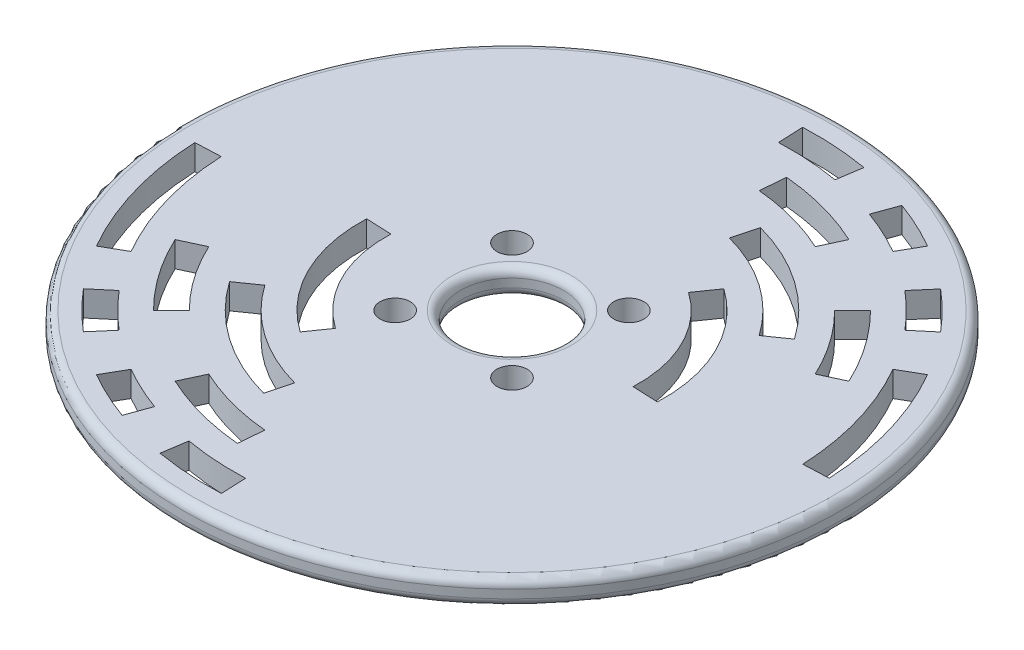
SolidWorks part; units mm, degrees
ref_plane "Front Plane" through (0, 0, 0) normal (0, 0, 1) x (1, 0, 0)
ref_plane "Top Plane" through (0, 0, 0) normal (0, 1, 0) x (1, 0, 0)
ref_plane "Right Plane" through (0, 0, 0) normal (1, 0, 0) x (0, 0, -1)
sketch "Sketch1" plane through (0, 0, 0) normal (0, 1, 0) x (1, 0, 0)
  line L0 (0, 0) -> (8.1776, 8.1776) construction
  circle A0 centre (0, 0) radius 6.096
  circle A1 centre (6.9148, 6.9148) radius 1.7859
  circle A2 centre (6.9148, -6.9148) radius 1.7859
  circle A3 centre (-6.9148, -6.9148) radius 1.7859
  circle A4 centre (-6.9148, 6.9148) radius 1.7859
  point P18 (0, 0)
  dimension "D2" = 3.5719
  dimension "D3" = 4
sketch "Sketch3" plane through (0, 0, 0) normal (0, 1, 0) x (1, 0, 0)
  line L0 (0, -36) -> (0, 36) construction
  line L2 (-36, 0) -> (36, 0) construction
  line L8 (8.6036, 12.2873) -> (10.3244, 14.7447) construction
  line L15 (32.9686, 1.4394) -> (35.9657, 1.5703)
  line L17 (-1.5703, 35.9657) -> (-1.4394, 32.9686)
  line L18 (6.1868, 35.4644) -> (5.7304, 32.4987)
  line L19 (12.3127, 33.8289) -> (11.2867, 31.0099)
  line L20 (18, 31.1769) -> (16.5, 28.5788)
  line L23 (14.9857, -0.6543) -> (17.9829, -0.7851) construction
  line L24 (23.1635, 27.5582) -> (21.212, 25.2795)
  line L25 (27.5776, 23.1404) -> (25.2795, 21.212)
  line L26 (31.1769, 18) -> (28.5788, 16.5)
  line L28 (14.9857, -0.6543) -> (17.9829, -0.7851)
  line L29 (11.2867, 31.0099) -> (12.3127, 33.8289) construction
  line L30 (10.3244, 14.7447) -> (8.6036, 12.2873)
  line L32 (16.5, 28.5788) -> (18, 31.1769) construction
  line L34 (23.3345, 23.3345) -> (25.4558, 25.4558) construction
  line L35 (25.2795, 21.212) -> (27.5776, 23.1404) construction
  line L36 (28.5788, 16.5) -> (31.1769, 18) construction
  line L37 (32.9686, 1.4394) -> (35.9657, 1.5703) construction
  line L38 (2.6147, 29.8858) -> (2.3532, 26.8973)
  line L39 (12.6785, 27.1892) -> (11.4107, 24.4703)
  line L40 (21.2132, 21.2132) -> (19.0919, 19.0919)
  line L41 (27.1892, 12.6785) -> (24.4703, 11.4107)
  line L42 (24.4703, 11.4107) -> (27.1892, 12.6785) construction
  line L43 (2.3532, 26.8973) -> (2.6147, 29.8858) construction
  line L44 (6.2117, 23.1822) -> (5.4352, 20.2844)
  line L45 (19.6596, 13.7658) -> (17.2022, 12.0451)
  line L46 (19.0919, 19.0919) -> (21.2132, 21.2132) construction
  line L47 (17.2022, 12.0451) -> (19.6596, 13.7658) construction
  line L48 (5.4352, 20.2844) -> (6.2117, 23.1822) construction
  line L49 (11.4107, 24.4703) -> (12.6785, 27.1892) construction
  line L64 (1.4394, -32.9686) -> (1.5703, -35.9657) construction
  line L65 (-8.6036, -12.2873) -> (-10.3244, -14.7447) construction
  line L67 (-11.2867, -31.0099) -> (-12.3127, -33.8289) construction
  line L68 (-16.5, -28.5788) -> (-18, -31.1769) construction
  line L69 (-23.3345, -23.3345) -> (-25.4558, -25.4558) construction
  line L70 (-25.2795, -21.212) -> (-27.5776, -23.1404) construction
  line L71 (-28.5788, -16.5) -> (-31.1769, -18) construction
  line L72 (-32.9686, -1.4394) -> (-35.9657, -1.5703) construction
  line L73 (-24.4703, -11.4107) -> (-27.1892, -12.6785) construction
  line L74 (-2.3532, -26.8973) -> (-2.6147, -29.8858) construction
  line L75 (-19.0919, -19.0919) -> (-21.2132, -21.2132) construction
  line L76 (-17.2022, -12.0451) -> (-19.6596, -13.7658) construction
  line L77 (-5.4352, -20.2844) -> (-6.2117, -23.1822) construction
  line L78 (-11.4107, -24.4703) -> (-12.6785, -27.1892) construction
  line L79 (-1.4394, -32.9686) -> (-1.5703, -35.9657) construction
  line L80 (-32.9686, -1.4394) -> (-35.9657, -1.5703)
  line L81 (1.5703, -35.9657) -> (1.4394, -32.9686)
  line L82 (-6.1868, -35.4644) -> (-5.7304, -32.4987)
  line L83 (-12.3127, -33.8289) -> (-11.2867, -31.0099)
  line L84 (-18, -31.1769) -> (-16.5, -28.5788)
  line L85 (-23.1635, -27.5582) -> (-21.212, -25.2795)
  line L86 (-27.5776, -23.1404) -> (-25.2795, -21.212)
  line L87 (-31.1769, -18) -> (-28.5788, -16.5)
  line L88 (-14.9857, 0.6543) -> (-17.9829, 0.7851)
  line L89 (-10.3244, -14.7447) -> (-8.6036, -12.2873)
  line L90 (-2.6147, -29.8858) -> (-2.3532, -26.8973)
  line L91 (-12.6785, -27.1892) -> (-11.4107, -24.4703)
  line L92 (-21.2132, -21.2132) -> (-19.0919, -19.0919)
  line L93 (-27.1892, -12.6785) -> (-24.4703, -11.4107)
  line L94 (-6.2117, -23.1822) -> (-5.4352, -20.2844)
  line L95 (-19.6596, -13.7658) -> (-17.2022, -12.0451)
  arc A0 (14.9857, -0.6543) -> (8.6036, 12.2873) centre (0, 0) ccw
  arc A1 (17.9829, -0.7851) -> (10.3244, 14.7447) centre (0, 0) ccw
  arc A4 (24.4703, 11.4107) -> (19.0919, 19.0919) centre (0, 0) ccw
  arc A5 (27.1892, 12.6785) -> (21.2132, 21.2132) centre (0, 0) ccw
  arc A6 (32.9686, 1.4394) -> (28.5788, 16.5) centre (0, 0) ccw
  arc A7 (35.9657, 1.5703) -> (31.1769, 18) centre (0, 0) ccw
  arc A8 (25.2795, 21.212) -> (21.212, 25.2795) centre (0, 0) ccw
  arc A9 (27.5776, 23.1404) -> (23.1635, 27.5582) centre (0, 0) ccw
  arc A10 (18, 31.1769) -> (12.3127, 33.8289) centre (0, 0) ccw
  arc A11 (16.5, 28.5788) -> (11.2867, 31.0099) centre (0, 0) ccw
  arc A12 (6.1868, 35.4644) -> (-1.5703, 35.9657) centre (0, 0) ccw
  arc A13 (5.7304, 32.4987) -> (-1.4394, 32.9686) centre (0, 0) ccw
  arc A14 (17.2022, 12.0451) -> (5.4352, 20.2844) centre (0, 0) ccw
  arc A15 (19.6596, 13.7658) -> (6.2117, 23.1822) centre (0, 0) ccw
  arc A16 (11.4107, 24.4703) -> (2.3532, 26.8973) centre (0, 0) ccw
  arc A17 (12.6785, 27.1892) -> (2.6147, 29.8858) centre (0, 0) ccw
  arc A32 (-14.9857, 0.6543) -> (-8.6036, -12.2873) centre (0, 0) ccw
  arc A33 (-17.9829, 0.7851) -> (-10.3244, -14.7447) centre (0, 0) ccw
  arc A34 (-24.4703, -11.4107) -> (-19.0919, -19.0919) centre (0, 0) ccw
  arc A35 (-27.1892, -12.6785) -> (-21.2132, -21.2132) centre (0, 0) ccw
  arc A36 (-32.9686, -1.4394) -> (-28.5788, -16.5) centre (0, 0) ccw
  arc A37 (-35.9657, -1.5703) -> (-31.1769, -18) centre (0, 0) ccw
  arc A38 (-25.2795, -21.212) -> (-21.212, -25.2795) centre (0, 0) ccw
  arc A39 (-27.5776, -23.1404) -> (-23.1635, -27.5582) centre (0, 0) ccw
  arc A40 (-18, -31.1769) -> (-12.3127, -33.8289) centre (0, 0) ccw
  arc A41 (-16.5, -28.5788) -> (-11.2867, -31.0099) centre (0, 0) ccw
  arc A42 (-6.1868, -35.4644) -> (1.5703, -35.9657) centre (0, 0) ccw
  arc A43 (-5.7304, -32.4987) -> (1.4394, -32.9686) centre (0, 0) ccw
  arc A44 (-17.2022, -12.0451) -> (-5.4352, -20.2844) centre (0, 0) ccw
  arc A45 (-19.6596, -13.7658) -> (-6.2117, -23.1822) centre (0, 0) ccw
  arc A46 (-11.4107, -24.4703) -> (-2.3532, -26.8973) centre (0, 0) ccw
  arc A47 (-12.6785, -27.1892) -> (-2.6147, -29.8858) centre (0, 0) ccw
sketch "Sketch4" plane through (0, 0, 0) normal (0, 1, 0) x (1, 0, 0)
  circle A0 centre (0, 0) radius 39
extrude "Boss-Extrude1" add sketch "Sketch4" along normal blind 3
extrude "Cut-Extrude1" cut sketch "Sketch3" along normal blind 3
extrude "Cut-Extrude3" cut sketch "Sketch1" along normal blind 3
fillet "Fillet1" radius 1 4 edges at (0, 0, 6.096) (0, 3, 6.096) (0, 3, 39) (0, 0, 39)
